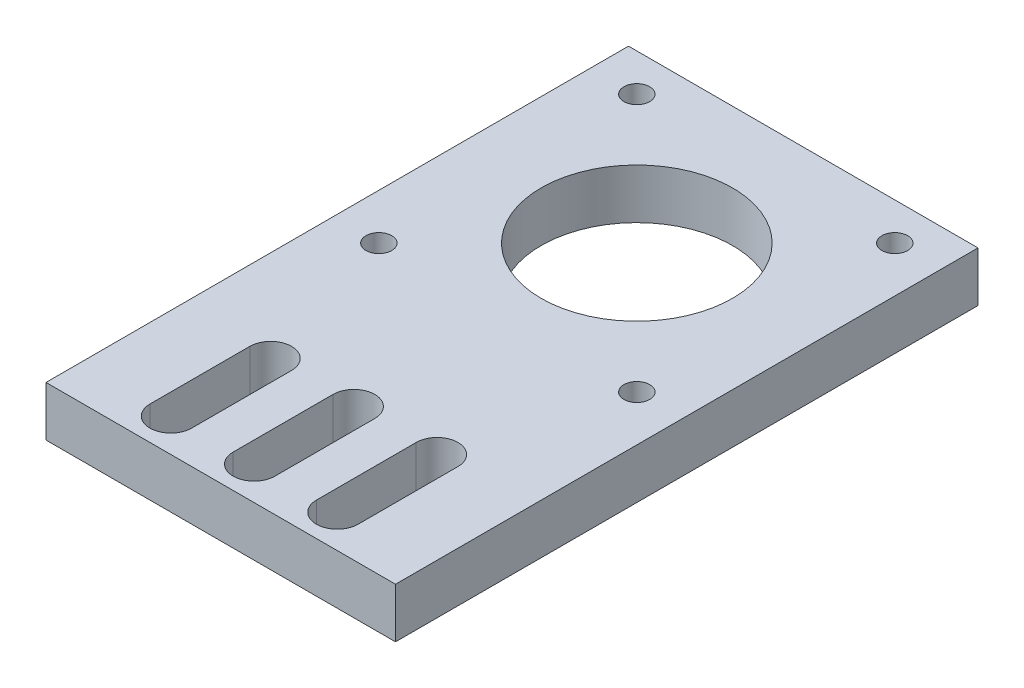
SolidWorks part; units mm, degrees
ref_plane "Front Plane" through (0, 0, 0) normal (0, 0, 1) x (1, 0, 0)
ref_plane "Top Plane" through (0, 0, 0) normal (0, 1, 0) x (1, 0, 0)
ref_plane "Right Plane" through (0, 0, 0) normal (1, 0, 0) x (0, 0, -1)
sketch "Sketch1" plane through (0, 0, 0) normal (0, 1, 0) x (1, 0, 0)
  line L0 (-21, -35) -> (21, -35)
  line L1 (-21, -35) -> (-21, 35)
  line L2 (-21, 35) -> (21, 35)
  line L3 (21, -35) -> (21, 35)
  line L4 (-21, -35) -> (21, 35) construction
  line L5 (-21, 35) -> (21, -35) construction
  line L6 (15.5, -0.5) -> (-15.5, -0.5) construction
  line L7 (15.5, -0.5) -> (15.5, 30.5) construction
  line L8 (15.5, 30.5) -> (-15.5, 30.5) construction
  line L9 (-15.5, -0.5) -> (-15.5, 30.5) construction
  line L10 (15.5, -0.5) -> (-15.5, 30.5) construction
  line L11 (15.5, 30.5) -> (-15.5, -0.5) construction
  line L14 (-7.49, -31) -> (-7.49, -19)
  line L16 (-12.51, -31) -> (-12.51, -19)
  line L17 (-7.49, -31) -> (-12.51, -19) construction
  line L18 (-7.49, -19) -> (-12.51, -31) construction
  line L20 (-2.51, -31) -> (-2.51, -19)
  line L22 (2.51, -31) -> (2.51, -19)
  line L23 (-2.51, -31) -> (2.51, -19) construction
  line L24 (-2.51, -19) -> (2.51, -31) construction
  line L26 (7.49, -31) -> (7.49, -19)
  line L28 (12.51, -31) -> (12.51, -19)
  line L29 (7.49, -31) -> (12.51, -19) construction
  line L30 (7.49, -19) -> (12.51, -31) construction
  circle A0 centre (0, 15) radius 11.5
  circle A1 centre (-15.5, 30.5) radius 1.55
  circle A2 centre (15.5, 30.5) radius 1.55
  circle A3 centre (15.5, -0.5) radius 1.55
  circle A4 centre (-15.5, -0.5) radius 1.55
  arc A5 (-12.51, -19) -> (-7.49, -19) centre (-10, -19) cw
  arc A6 (-12.51, -31) -> (-7.49, -31) centre (-10, -31) ccw
  arc A7 (-2.51, -19) -> (2.51, -19) centre (0, -19) cw
  arc A8 (-2.51, -31) -> (2.51, -31) centre (0, -31) ccw
  arc A9 (7.49, -19) -> (12.51, -19) centre (10, -19) cw
  arc A10 (7.49, -31) -> (12.51, -31) centre (10, -31) ccw
  point P0 (0, 0)
  point P15 (0, -25)
  point P16 (-10, -25)
  point P20 (10, -25)
  point P22 (0, -25)
  point P25 (-10, -25)
  point P28 (10, -25)
  dimension "D1" = 23
  dimension "D6" = 3.1
  dimension "D7" = 2.51
  dimension "D2" = 20
  dimension "D3" = 70
  dimension "D4" = 42
  dimension "D5" = 31
  dimension "D8" = 10
  dimension "D9" = 12
  dimension "D10" = 10
  dimension "D11" = 10
extrude "Boss-Extrude1" add sketch "Sketch1" along normal blind 6
